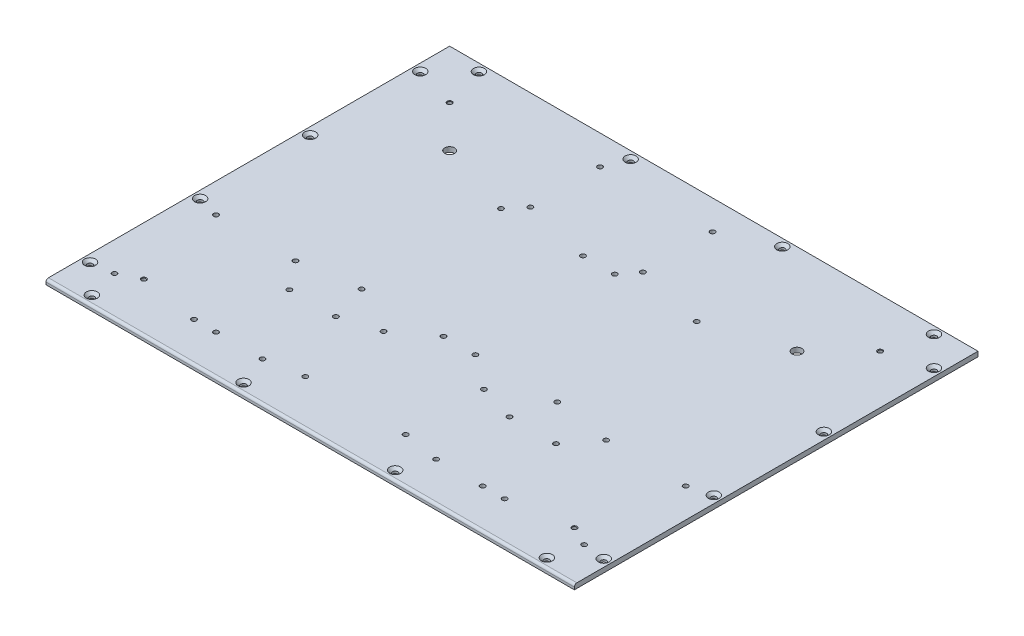
SolidWorks part; units mm, degrees
material "6061 合金"
ref_plane "前基準面" through (0, 0, 0) normal (0, 0, 1) x (1, 0, 0)
ref_plane "上基準面" through (0, 0, 0) normal (0, 1, 0) x (1, 0, 0)
ref_plane "右基準面" through (0, 0, 0) normal (1, 0, 0) x (0, 0, -1)
sketch "草圖1" plane through (0, 0, 0) normal (0, 1, 0) x (1, 0, 0)
  line L1 (0, 0) -> (432, 0)
  line L2 (0, 0) -> (0, 330)
  line L3 (0, 330) -> (432, 330)
  line L4 (432, 0) -> (432, 330)
  dimension "D1" = 432
  dimension "D2" = 330
extrude "填料-伸長1" add sketch "草圖1" along normal blind 4
hole_wizard "M4 六角凹錐坑螺釘的錐孔1" positions "草圖3" profile "草圖2" countersink size "M4" standard "Iso" end condition through all
sketch "草圖3" plane through (0, 4, 0) normal (0, 1, 0) x (1, 0, 0)
  line L0 (432, 330) -> (0, 330) construction
  line L2 (0, 330) -> (0, 0) construction
  line L3 (0, 0) -> (432, 0) construction
  line L5 (432, 0) -> (432, 330) construction
  point P0 (6, 300)
  point P2 (6, 210)
  point P4 (6, 120)
  point P6 (6, 30)
  point P8 (30, 7.5)
  point P10 (154, 7.5)
  point P12 (278, 7.5)
  point P14 (402, 7.5)
  point P16 (426, 30)
  point P18 (426, 120)
  point P20 (426, 210)
  point P22 (426, 300)
  point P24 (402, 324)
  point P26 (278, 324)
  point P28 (154, 324)
  point P30 (30, 324)
  dimension "D1" = 30
  dimension "D2" = 90
  dimension "D3" = 90
  dimension "D4" = 90
  dimension "D5" = 6
  dimension "D6" = 30
  dimension "D7" = 124
  dimension "D8" = 124
  dimension "D9" = 124
  dimension "D10" = 7.5
  dimension "D11" = 30
  dimension "D12" = 124
  dimension "D13" = 124
  dimension "D14" = 124
  dimension "D15" = 6
  dimension "D16" = 30
  dimension "D17" = 90
  dimension "D18" = 90
  dimension "D19" = 90
  dimension "D20" = 6
sketch "草圖2" plane through (6, 4, -300) normal (1, 0, 0) x (0, 0, 1)
  line L0 (0, 0) -> (0, 4)
  line L1 (0, 4) -> (2.25, 4)
  line L2 (2.25, 4) -> (2.25, 2.23)
  line L3 (2.25, 2.23) -> (4.48, 0)
  line L5 (4.48, 0) -> (0, 0)
  line L6 (-2.25, 2.23) -> (-4.48, 0) construction
  line L11 (0, -6.35) -> (0, 107.95) construction
  dimension "貫穿孔直徑" = 4.5
  dimension "貫穿孔深度" = 4
  dimension "近端錐孔直徑" = 8.96
  dimension "近端錐孔角度" = 90
fillet "圓角1" radius 2 1 edges at (216, 4, 0)
hole_wizard "Ø8.0 (8) 直徑孔2" positions "草圖8" profile "草圖7" hole size "Ø8.0" standard "Iso" end condition through all
sketch "草圖8" plane through (0, 0, 0) normal (0, -1, 0) x (-1, 0, 0)
  line L0 (-216, 0) -> (-216, 330) construction
  line L1 (0, 0) -> (-432, 0) construction
  line L2 (-432, 330) -> (0, 330) construction
  line L3 (0, 330) -> (0, 0) construction
  point P8 (-74, 256)
  point P13 (-358, 256)
  dimension "D1" = 74
  dimension "D2" = 74
sketch "草圖7" plane through (74, 0, -256) normal (1, 0, 0) x (0, 0, -1)
  line L0 (0, 0) -> (0, 4)
  line L1 (0, 4) -> (4, 4)
  line L2 (4, 4) -> (4, 0)
  line L5 (4, 0) -> (0, 0)
  line L11 (0, -6.35) -> (0, 107.95) construction
  dimension "貫穿孔直徑" = 8
  dimension "貫穿孔深度" = 4
hole_wizard "Ø4.0 (4) 直徑孔1" positions "草圖10" profile "草圖9" hole size "Ø4.0" standard "Iso"
sketch "草圖10" plane through (0, 0, 0) normal (0, -1, 0) x (-1, 0, 0)
  line L0 (-216, 0) -> (-216, 330) construction
  line L1 (0, 0) -> (-432, 0) construction
  line L2 (-432, 330) -> (0, 330) construction
  line L4 (0, 330) -> (0, 0) construction
  point P0 (-107, 32)
  point P2 (-145, 32)
  point P4 (-107, 92)
  point P6 (-145, 92)
  point P8 (-147, 249)
  point P10 (-239, 249)
  point P12 (-239, 306)
  point P14 (-147, 306)
  point P26 (-287, 92)
  point P27 (-325, 92)
  point P28 (-287, 32)
  point P29 (-325, 32)
  dimension "D1" = 107
  dimension "D2" = 38
  dimension "D3" = 60
  dimension "D4" = 57
  dimension "D5" = 92
  dimension "D6" = 24
  dimension "D7" = 147
  dimension "D8" = 32
sketch "草圖9" plane through (107, 0, -32) normal (1, 0, 0) x (0, 0, -1)
  line L0 (0, 0) -> (0, 6.2017)
  line L1 (0, 6.2017) -> (2, 5)
  line L2 (2, 5) -> (2, 0)
  line L5 (2, 0) -> (0, 0)
  line L10 (0, 6.2017) -> (-2, 5) construction
  line L11 (0, -6.35) -> (0, 107.95) construction
  dimension "鑽孔直徑" = 4
  dimension "鑽孔深度" = 5
  dimension "導頭角度" = 118
hole_wizard "M4 螺紋孔1" positions "草圖12" profile "草圖11" tap size "M4" standard "Iso" end condition through all
sketch "草圖12" plane through (0, 4, 0) normal (0, 1, 0) x (1, 0, 0)
  line L0 (432, 330) -> (0, 330) construction
  line L1 (0, 330) -> (0, 2) construction
  line L2 (432, 2) -> (432, 330) construction
  line L3 (0, 0) -> (432, 0) construction
  point P0 (40, 290)
  point P2 (40, 40)
  point P4 (392, 40)
  point P6 (392, 290)
  dimension "D1" = 40
  dimension "D2" = 40
  dimension "D3" = 40
  dimension "D4" = 40
sketch "草圖11" plane through (40, 4, -290) normal (1, 0, 0) x (0, 0, 1)
  line L0 (0, 0) -> (0, 4)
  line L1 (0, 4) -> (1.65, 4)
  line L2 (1.65, 4) -> (1.65, 0.375)
  line L3 (1.65, 0.375) -> (2.025, 0)
  line L5 (2.025, 0) -> (0, 0)
  line L6 (-1.65, 0.375) -> (-2.025, 0) construction
  line L11 (0, -6.35) -> (0, 107.95) construction
  dimension "貫穿螺孔鑽直徑" = 3.3
  dimension "貫穿螺孔鑽深度" = 4
  dimension "近端錐孔直徑" = 4.05
  dimension "近端錐孔角度" = 90
cosmetic thread "鑽孔螺紋1" parameters "D2"=4
cosmetic thread "鑽孔螺紋2" parameters "D2"=4
cosmetic thread "鑽孔螺紋3" parameters "D2"=4
cosmetic thread "鑽孔螺紋4" parameters "D2"=4
hole_wizard "Ø4.0 (4) 直徑孔2" positions "草圖14" profile "草圖13" hole size "Ø4.0" standard "Iso" end condition through all
sketch "草圖14" plane through (0, 0, 0) normal (0, -1, 0) x (-1, 0, 0)
  line L0 (0, 0) -> (-432, 0) construction
  line L1 (0, 330) -> (0, 0) construction
  line L2 (-216, 0) -> (-216, 330) construction
  line L3 (-432, 330) -> (0, 330) construction
  point P0 (-24, 32)
  point P2 (-89, 32)
  point P4 (-24, 115)
  point P6 (-89, 115)
  point P8 (-203, 122)
  point P10 (-203, 236)
  point P12 (-136, 236)
  point P14 (-136, 122)
  point P28 (-229, 122)
  point P29 (-296, 236)
  point P30 (-296, 122)
  point P31 (-408, 32)
  point P32 (-408, 115)
  point P33 (-343, 115)
  point P34 (-343, 32)
  point P35 (-229, 236)
  dimension "D1" = 32
  dimension "D2" = 83
  dimension "D3" = 65
  dimension "D4" = 24
  dimension "D5" = 67
  dimension "D6" = 122
  dimension "D7" = 114
  dimension "D8" = 136
sketch "草圖13" plane through (24, 0, -32) normal (1, 0, 0) x (0, 0, -1)
  line L0 (0, 0) -> (0, 4)
  line L1 (0, 4) -> (2, 4)
  line L2 (2, 4) -> (2, 0)
  line L5 (2, 0) -> (0, 0)
  line L11 (0, -6.35) -> (0, 107.95) construction
  dimension "貫穿孔直徑" = 4
  dimension "貫穿孔深度" = 4
hole_wizard "Ø4.0 (4) 直徑孔3" positions "草圖16" profile "草圖15" hole size "Ø4.0" standard "Iso"
sketch "草圖16" plane through (0, 0, 0) normal (0, -1, 0) x (-1, 0, 0)
  line L0 (0, 330) -> (0, 0) construction
  line L2 (0, 0) -> (-432, 0) construction
  point P0 (-175, 37)
  point P2 (-257, 37)
  point P4 (-175, 101)
  point P6 (-257, 101)
  dimension "D1" = 64
  dimension "D2" = 82
  dimension "D3" = 175
  dimension "D4" = 37
sketch "草圖15" plane through (175, 0, -37) normal (1, 0, 0) x (0, 0, -1)
  line L0 (0, 0) -> (0, 6.2017)
  line L1 (0, 6.2017) -> (2, 5)
  line L2 (2, 5) -> (2, 0)
  line L5 (2, 0) -> (0, 0)
  line L10 (0, 6.2017) -> (-2, 5) construction
  line L11 (0, -6.35) -> (0, 107.95) construction
  dimension "鑽孔直徑" = 4
  dimension "鑽孔深度" = 5
  dimension "導頭角度" = 118
